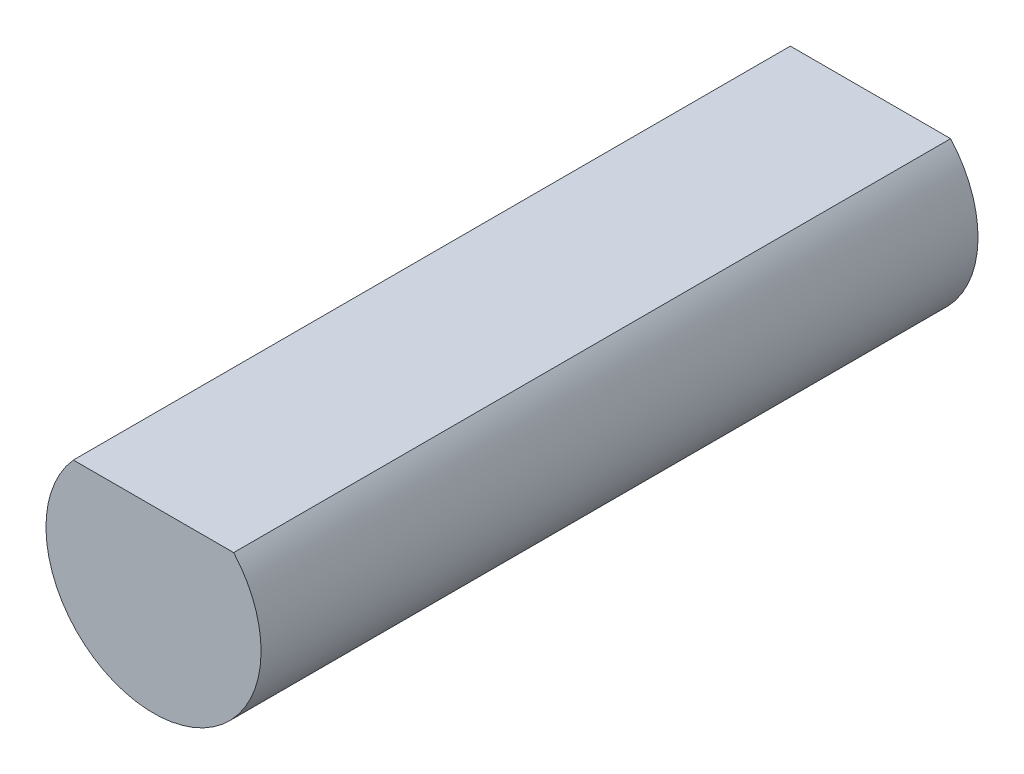
SolidWorks part; units mm, degrees
ref_plane "前视基准面" through (0, 0, 0) normal (0, 0, 1) x (1, 0, 0)
ref_plane "上视基准面" through (0, 0, 0) normal (0, 1, 0) x (1, 0, 0)
ref_plane "右视基准面" through (0, 0, 0) normal (1, 0, 0) x (0, 0, -1)
sketch "草图1" plane through (0, 0, 0) normal (0, 0, 1) x (1, 0, 0)
  circle A0 centre (0, 0) radius 1.5
extrude "凸台-拉伸1" add sketch "草图1" along normal blind 10
sketch "草图2" plane through (0, 0, 10) normal (0, 0, 1) x (1, 0, 0)
  line L0 (0, 0) -> (0, 1)
  line L1 (-1.118, 1) -> (1.118, 1)
  circle A1 centre (0, 0) radius 1.5 construction
  dimension "D1" = 1
extrude "切除-拉伸1" cut sketch "草图2" against normal blind 10
